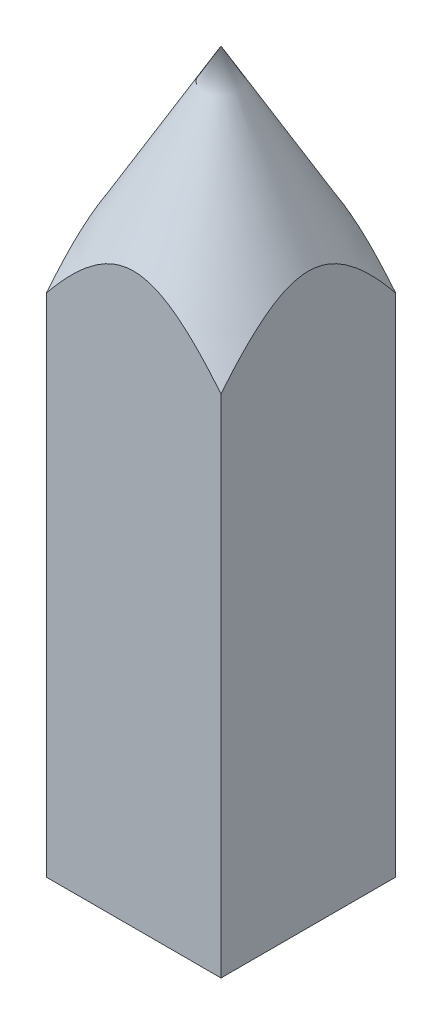
SolidWorks part; units mm, degrees
ref_plane "Front" through (0, 0, 0) normal (0, 0, 1) x (1, 0, 0)
ref_plane "Top" through (0, 0, 0) normal (0, 1, 0) x (1, 0, 0)
ref_plane "Right" through (0, 0, 0) normal (1, 0, 0) x (0, 0, -1)
sketch "Sketch4" plane through (0, 0, 0) normal (0, 0, 1) x (1, 0, 0)
  line L0 (0, 0) -> (0, 41.2053)
  line L1 (0, 41.2053) -> (7.0711, 28.9578)
  line L2 (7.0711, 28.9578) -> (7.0711, 0)
  line L4 (7.0711, 0) -> (0, 0)
  dimension "D1" = 41.2053
  dimension "D2" = 7.0711
  dimension "D3" = 30
revolve "Revolve1" add sketch "Sketch4" angle 360 about L0
sketch "Sketch5" plane through (0, 0, 0) normal (0, 1, 0) x (1, 0, 0)
  line L1 (-5, 5) -> (5, 5)
  line L2 (-5, 5) -> (-5, -5)
  line L3 (-5, -5) -> (5, -5)
  line L4 (5, 5) -> (5, -5)
  circle A4 centre (0, 0) radius 7.0711 construction
extrude "Extrude2" cut sketch "Sketch5" along normal through all flip side to cut
